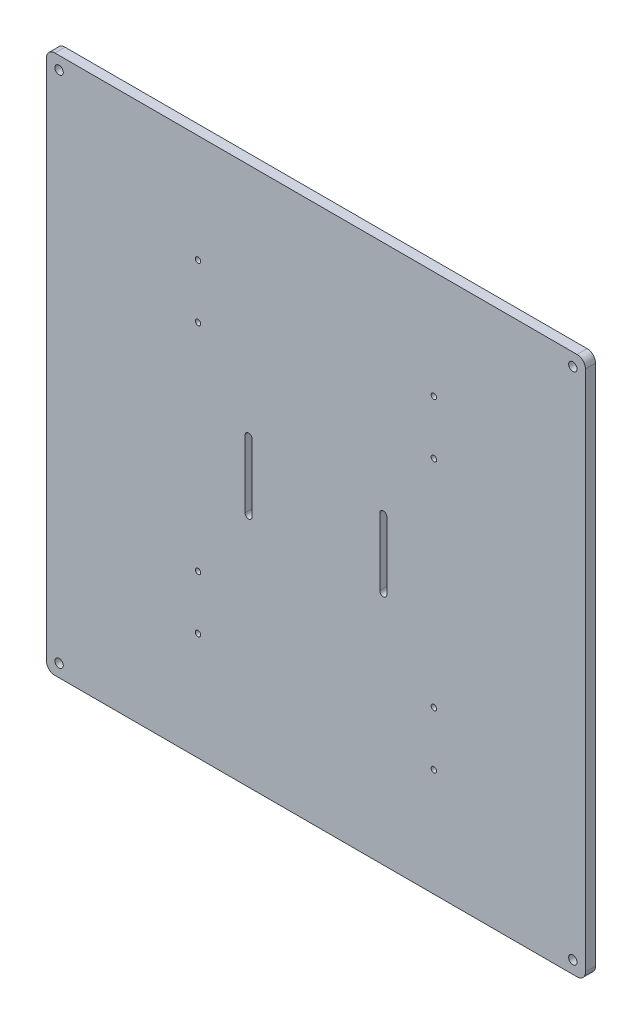
SolidWorks part; units mm, degrees
ref_plane "Plan de face" through (0, 0, 0) normal (0, 0, 1) x (1, 0, 0)
ref_plane "Plan de dessus" through (0, 0, 0) normal (0, 1, 0) x (1, 0, 0)
ref_plane "Plan de droite" through (0, 0, 0) normal (1, 0, 0) x (0, 0, -1)
sketch "Esquisse1" plane through (0, 0, 0) normal (0, 0, 1) x (1, 0, 0)
  line L0 (160, 320) -> (160, 0) construction
  line L1 (0, 0) -> (320, 0)
  line L2 (0, 0) -> (0, 320)
  line L3 (0, 320) -> (320, 320)
  line L4 (320, 0) -> (320, 320)
  line L5 (160, 0) -> (320, 160) construction
  line L6 (320, 160) -> (0, 160) construction
  circle A0 centre (7.5, 312.5) radius 2.5
  circle A1 centre (312.5, 312.5) radius 2.5
  circle A2 centre (7.5, 7.5) radius 2.5
  circle A3 centre (312.5, 7.5) radius 2.5
  dimension "D2" = 7.5
  dimension "D4" = 5
  dimension "D1" = 320
  dimension "D3" = 7.5
extrude "Boss.-Extru.1" add sketch "Esquisse1" along normal blind 6
fillet "Congé3" radius 5 1 edges at (0, 320, 3)
fillet "Congé4" radius 5 1 edges at (0, 0, 3)
fillet "Congé5" radius 5 1 edges at (320, 320, 3)
fillet "Congé6" radius 5 1 edges at (320, 0, 3)
sketch "Sketch1" plane through (0, 0, 6) normal (0, 0, 1) x (1, 0, 0)
  line L0 (0, 160) -> (320, 160) construction
  line L1 (0, 5) -> (0, 315) construction
  line L2 (320, 5) -> (320, 315) construction
  line L3 (160, 320) -> (160, 0) construction
  line L4 (5, 320) -> (315, 320) construction
  line L5 (5, 0) -> (315, 0) construction
  circle A0 centre (90, 224) radius 1.6
  circle A1 centre (230, 224) radius 1.6
  circle A2 centre (90, 96) radius 1.6
  circle A3 centre (230, 96) radius 1.6
  circle A4 centre (90, 256) radius 1.6
  circle A5 centre (90, 64) radius 1.6
  circle A6 centre (230, 64) radius 1.6
  circle A7 centre (230, 256) radius 1.6
  dimension "D1" = 3.2
  dimension "D2" = 3.2
  dimension "D3" = 3.2
  dimension "D4" = 3.2
  dimension "D13" = 3.2
  dimension "D14" = 3.2
  dimension "D15" = 3.2
  dimension "D16" = 3.2
  dimension "D5" = 128
  dimension "D6" = 128
  dimension "D7" = 64
  dimension "D8" = 64
  dimension "D9" = 140
  dimension "D10" = 140
  dimension "D11" = 70
  dimension "D12" = 70
  dimension "D17" = 32
  dimension "D18" = 32
  dimension "D19" = 32
  dimension "D20" = 32
  dimension "D21" = 70
  dimension "D22" = 70
  dimension "D23" = 70
  dimension "D24" = 70
extrude "Cut-Extrude1" cut sketch "Sketch1" against normal through all
sketch "Sketch3" plane through (0, 0, 0) normal (0, 0, -1) x (-1, 0, 0)
  line L0 (-160, 320) -> (-160, 0) construction
  line L1 (-5, 320) -> (-315, 320) construction
  line L2 (-5, 0) -> (-315, 0) construction
  line L3 (-320, 160) -> (0, 160) construction
  line L4 (-320, 5) -> (-320, 315) construction
  line L5 (0, 5) -> (0, 315) construction
  line L6 (-200, 180) -> (-200, 140) construction
  line L7 (-197.9, 180) -> (-197.9, 140)
  line L8 (-202.1, 180) -> (-202.1, 140)
  line L9 (-120, 180) -> (-120, 140) construction
  line L10 (-117.9, 180) -> (-117.9, 140)
  line L11 (-122.1, 180) -> (-122.1, 140)
  arc A0 (-197.9, 180) -> (-202.1, 180) centre (-200, 180) ccw
  arc A1 (-202.1, 140) -> (-197.9, 140) centre (-200, 140) ccw
  arc A2 (-117.9, 180) -> (-122.1, 180) centre (-120, 180) ccw
  arc A3 (-122.1, 140) -> (-117.9, 140) centre (-120, 140) ccw
  point P14 (-200, 160)
  point P19 (-120, 160)
  dimension "D1" = 2.1
  dimension "D2" = 2.1
  dimension "D3" = 40
  dimension "D4" = 20
  dimension "D5" = 20
  dimension "D6" = 40
  dimension "D7" = 80
  dimension "D8" = 40
extrude "Cut-Extrude2" cut sketch "Sketch3" against normal through all
